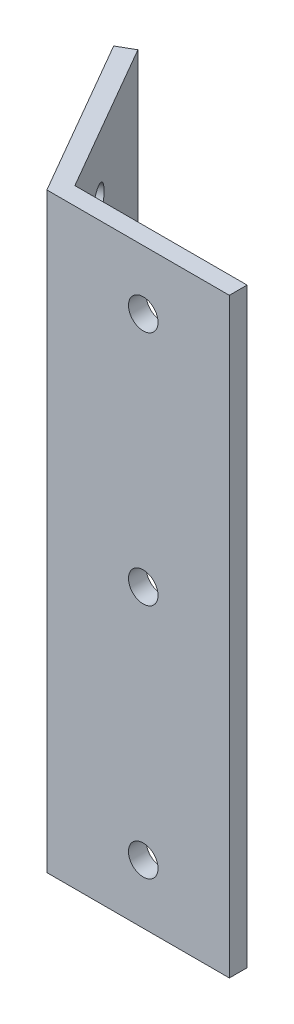
SolidWorks part; units mm, degrees
ref_plane "Front Plane" through (0, 0, 0) normal (0, 0, 1) x (1, 0, 0)
ref_plane "Top Plane" through (0, 0, 0) normal (0, 1, 0) x (1, 0, 0)
ref_plane "Right Plane" through (0, 0, 0) normal (1, 0, 0) x (0, 0, -1)
sketch "Sketch1" plane through (0, 0, 0) normal (0, 1, 0) x (1, 0, 0)
  line L0 (0, 0) -> (30, 0)
  line L1 (0, 0) -> (-15, 25.9808)
  dimension "D1" = 30
extrude "Extrude-Thin1" add sketch "Sketch1" along normal blind 100 thin thin type mid plane wall 3
sketch "Sketch2" plane through (1.299, 0, -0.75) normal (0.866, 0, -0.5) x (-0.5, 0, -0.866)
  line L0 (11.866, 90) -> (11.866, 10) construction
  line L1 (0.866, 100) -> (30, 100) construction
  line L2 (0.866, 0) -> (30, 0) construction
  line L5 (0.866, 100) -> (0.866, 0) construction
  circle A0 centre (11.866, 90) radius 2.5
  circle A1 centre (11.866, 50) radius 2.5
  circle A2 centre (11.866, 10) radius 2.5
  dimension "D1" = 5
  dimension "D2" = 10
  dimension "D3" = 10
  dimension "D4" = 11
extrude "Cut-Extrude1" cut sketch "Sketch2" against normal blind 10
sketch "Sketch3" plane through (0, 0, -1.5) normal (0, 0, -1) x (-1, 0, 0)
  line L0 (-15.433, 100) -> (-15.433, 0) construction
  line L1 (-30, 100) -> (-0.866, 100) construction
  line L2 (-30, 0) -> (-0.866, 0) construction
  circle A0 centre (-15.433, 50) radius 2.5
  circle A1 centre (-15.433, 10) radius 2.5
  circle A2 centre (-15.433, 90) radius 2.5
  dimension "D1" = 5
  dimension "D2" = 10
  dimension "D3" = 10
extrude "Cut-Extrude2" cut sketch "Sketch3" against normal blind 10
